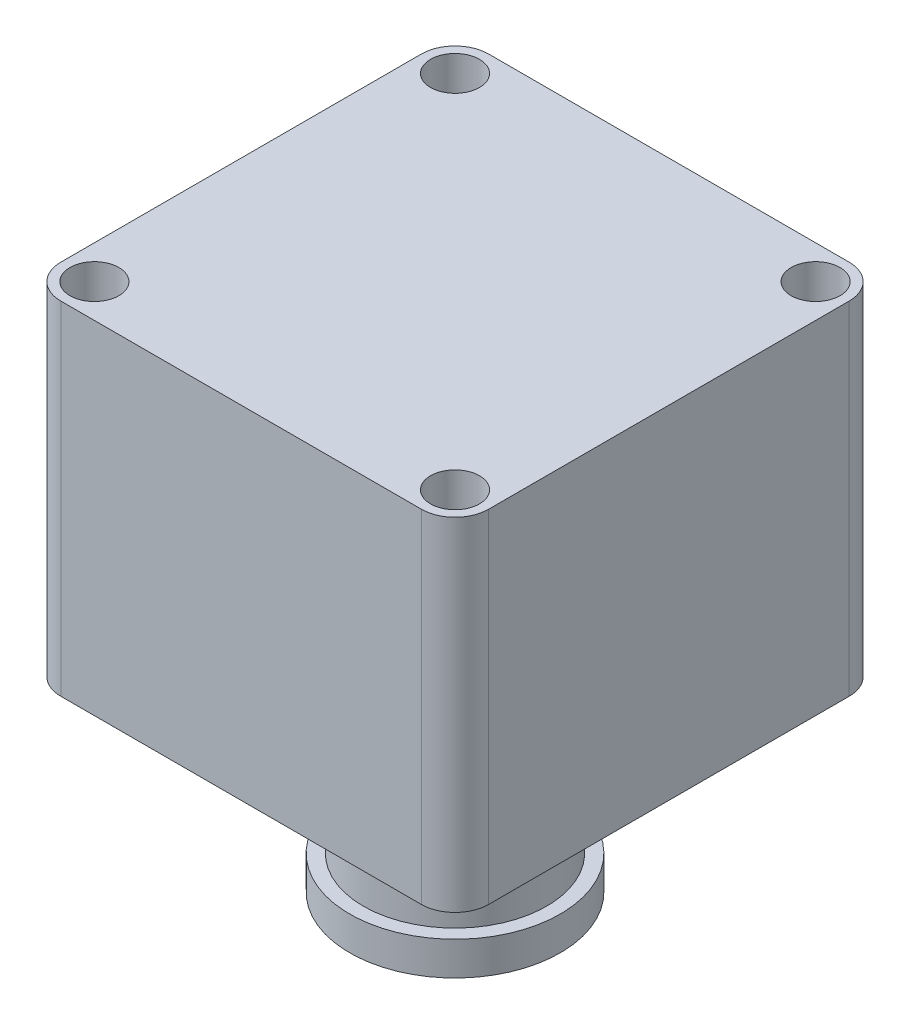
SolidWorks part; units mm, degrees
ref_plane "Front Plane" through (0, 0, 0) normal (0, 0, 1) x (1, 0, 0)
ref_plane "Top Plane" through (0, 0, 0) normal (0, 1, 0) x (1, 0, 0)
ref_plane "Right Plane" through (0, 0, 0) normal (1, 0, 0) x (0, 0, -1)
sketch "Sketch1" plane through (0, 0, 0) normal (0, 1, 0) x (1, 0, 0)
  line L1 (-80.1737, 32.5376) -> (-20.2297, 32.5376)
  line L2 (-85.7617, 26.9496) -> (-85.7617, -32.9944)
  line L3 (-80.1737, -38.5824) -> (-20.2297, -38.5824)
  line L4 (-14.6417, 26.9496) -> (-14.6417, -32.9944)
  arc A0 (-20.2297, -38.5824) -> (-14.6417, -32.9944) centre (-20.2297, -32.9944) ccw
  arc A1 (-85.7617, -32.9944) -> (-80.1737, -38.5824) centre (-80.1737, -32.9944) ccw
  arc A2 (-20.2297, 32.5376) -> (-14.6417, 26.9496) centre (-20.2297, 26.9496) cw
  arc A3 (-80.1737, 32.5376) -> (-85.7617, 26.9496) centre (-80.1737, 26.9496) ccw
  circle A4 centre (-80.1737, 26.9496) radius 4.064
  circle A5 centre (-80.1737, -32.9944) radius 4.064
  circle A6 centre (-20.2297, 26.9496) radius 4.064
  circle A7 centre (-20.2297, -32.9944) radius 4.064
  point P9 (-85.7617, -38.5824)
  point P12 (-14.6417, 32.5376)
  point P15 (-85.7617, 32.5376)
  dimension "D3" = 5.588
  dimension "D1" = 71.12
  dimension "D2" = 71.12
extrude "Boss-Extrude1" add sketch "Sketch1" along normal blind 56.896
sketch "Sketch2" plane through (0, 0, 0) normal (0, -1, 0) x (1, 0, 0)
  line L0 (-14.6417, 32.9944) -> (-14.6417, -26.9496) construction
  line L1 (-80.1737, 38.5824) -> (-20.2297, 38.5824) construction
  circle A0 centre (-50.2017, 3.0224) radius 15.24
  dimension "D1" = 35.56
  dimension "D2" = 35.56
extrude "Boss-Extrude2" add sketch "Sketch2" along normal blind 25.4 contours A0
sketch "Sketch3" plane through (0, -25.4, 0) normal (0, -1, 0) x (1, 0, 0)
  circle A0 centre (-50.2017, 3.0224) radius 17.5016
  circle A1 centre (-50.2017, 3.0224) radius 15.24 construction
  dimension "D1" = 0
extrude "Boss-Extrude3" add sketch "Sketch3" along normal blind 5.588 contours A0
